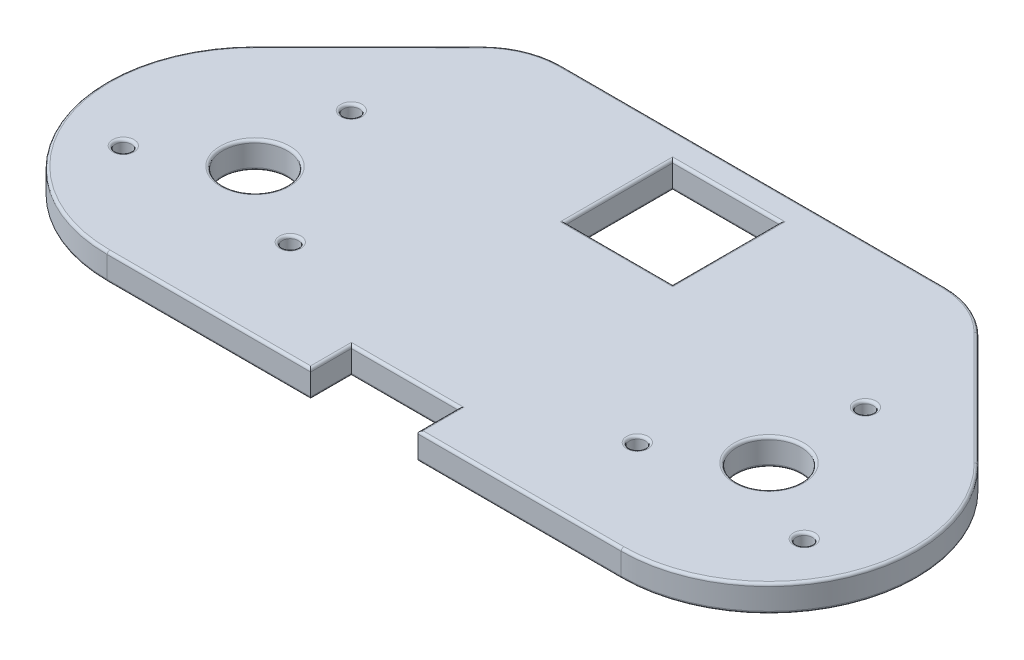
SolidWorks part; units mm, degrees
ref_plane "前视基准面" through (0, 0, 0) normal (0, 0, 1) x (1, 0, 0)
ref_plane "上视基准面" through (0, 0, 0) normal (0, 1, 0) x (1, 0, 0)
ref_plane "右视基准面" through (0, 0, 0) normal (1, 0, 0) x (0, 0, -1)
sketch "草图1" plane through (0, 0, 0) normal (0, 1, 0) x (1, 0, 0)
  line L0 (-46.1904, 14.9637) -> (49.8096, 14.9637) construction
  line L2 (-46.1904, -12.6363) -> (49.8096, -12.6363)
  line L3 (1.8096, 14.9637) -> (1.8096, 93.8376) construction
  line L4 (1.8096, 59.9637) -> (37.602, 59.9637)
  line L5 (1.8096, 59.9637) -> (-33.9827, 59.9637)
  line L6 (-44.5826, 55.577) -> (-65.6942, 34.4922)
  line L7 (48.2019, 55.577) -> (69.3134, 34.4922)
  line L9 (-8.1904, 54.9637) -> (11.8096, 54.9637)
  line L10 (-8.1904, 54.9637) -> (-8.1904, 34.9637)
  line L11 (-8.1904, 34.9637) -> (11.8096, 34.9637)
  line L12 (11.8096, 54.9637) -> (11.8096, 34.9637)
  line L13 (-8.1904, 54.9637) -> (11.8096, 34.9637) construction
  line L14 (-8.1904, 34.9637) -> (11.8096, 54.9637) construction
  arc A0 (-65.6942, 34.4922) -> (-46.1904, -12.6363) centre (-46.1904, 14.9637) ccw
  arc A1 (49.8096, -12.6363) -> (69.3134, 34.4922) centre (49.8096, 14.9637) ccw
  arc A2 (48.2019, 55.577) -> (37.602, 59.9637) centre (37.602, 44.9637) ccw
  arc A3 (-44.5826, 55.577) -> (-33.9827, 59.9637) centre (-33.9827, 44.9637) cw
  point P2 (0, 0)
  point P4 (1.8096, 44.9637)
  point P17 (43.8096, 59.9637)
  point P20 (-40.1904, 59.9637)
  dimension "D6" = 15
  dimension "D1" = 96
  dimension "D2" = 42
  dimension "D3" = 42
  dimension "D4" = 27.6
  dimension "D5" = 45
  dimension "D7" = 20
  dimension "D8" = 20
  dimension "D9" = 30
extrude "凸台-拉伸1" add sketch "草图1" along normal blind 5
sketch "草图2" plane through (0, 5, 0) normal (0, 1, 0) x (1, 0, 0)
  circle A0 centre (-46.1904, 14.9637) radius 6
  circle A1 centre (49.8096, 14.9637) radius 6
  dimension "D1" = 12
extrude "切除-拉伸1" cut sketch "草图2" against normal through all
sketch "草图3" plane through (0, 5, 0) normal (0, 1, 0) x (1, 0, 0)
  line L1 (-46.1904, 14.9637) -> (49.8096, 14.9637) construction
  line L3 (-8.1904, -25.0363) -> (11.8096, -25.0363)
  line L4 (-8.1904, -25.0363) -> (-8.1904, -5.0363)
  line L5 (-8.1904, -5.0363) -> (11.8096, -5.0363)
  line L6 (11.8096, -25.0363) -> (11.8096, -5.0363)
  line L7 (-8.1904, -25.0363) -> (11.8096, -5.0363) construction
  line L8 (-8.1904, -5.0363) -> (11.8096, -25.0363) construction
  point P0 (1.8096, -15.0363)
  dimension "D1" = 30
  dimension "D2" = 20
  dimension "D3" = 20
extrude "切除-拉伸2" cut sketch "草图3" against normal through all
sketch "草图4" plane through (0, 5, 0) normal (0, 1, 0) x (1, 0, 0)
  line L0 (49.8096, 14.9637) -> (49.8096, 32.9637) construction
  line L1 (1.8096, 54.9637) -> (1.8096, -5.0363) construction
  line L2 (11.8096, 54.9637) -> (-8.1904, 54.9637) construction
  line L3 (11.8096, -5.0363) -> (-8.1904, -5.0363) construction
  circle A0 centre (49.8096, 32.9637) radius 1.5
  circle A1 centre (65.3981, 5.9637) radius 1.5
  circle A2 centre (34.2212, 5.9637) radius 1.5
  circle A3 centre (-30.6019, 5.9637) radius 1.5
  circle A4 centre (-61.7788, 5.9637) radius 1.5
  circle A5 centre (-46.1904, 32.9637) radius 1.5
  point P10 (49.8096, 14.9637)
  dimension "D2" = 3
  dimension "D1" = 18
  dimension "D3" = 3
extrude "切除-拉伸3" cut sketch "草图4" against normal through all
fillet "圆角1" radius 0.5 48 edges at (1.8096, 0, -34.9637) (-8.1904, 0, -44.9637) (1.8096, 0, -54.9637) (11.8096, 0, -44.9637) (49.8096, 0, -8.9637) (-46.1904, 0, -8.9637) (75.312, 0, -4.4097) (58.7576, 0, -45.0346) (43.3378, 0, -58.8237) (1.8096, 0, -59.9637) (-39.7186, 0, -58.8237) (-55.1384, 0, -45.0346) (-71.6928, 0, -4.4097) (-27.1904, 0, 12.6363) (-8.1904, 0, 8.8363) (1.8096, 0, 5.0363) (11.8096, 0, 8.8363) (30.8096, 0, 12.6363) (49.8096, 0, -31.4637) (65.3981, 0, -4.4637) (34.2212, 0, -4.4637) (-30.6019, 0, -7.4637) (-61.7788, 0, -7.4637) (-46.1904, 0, -34.4637) (-8.1904, 5, -44.9637) (1.8096, 5, -34.9637) (11.8096, 5, -44.9637) (1.8096, 5, -54.9637) (49.8096, 5, -8.9637) (-46.1904, 5, -8.9637) (1.8096, 5, 5.0363) (-8.1904, 5, 8.8363) (-27.1904, 5, 12.6363) (-71.6928, 5, -4.4097) (-55.1384, 5, -45.0346) (-39.7186, 5, -58.8237) (1.8096, 5, -59.9637) (43.3378, 5, -58.8237) (58.7576, 5, -45.0346) (75.312, 5, -4.4097) (30.8096, 5, 12.6363) (11.8096, 5, 8.8363) (49.8096, 5, -31.4637) (65.3981, 5, -4.4637) (34.2212, 5, -4.4637) (-30.6019, 5, -7.4637) (-61.7788, 5, -7.4637) (-46.1904, 5, -34.4637)
